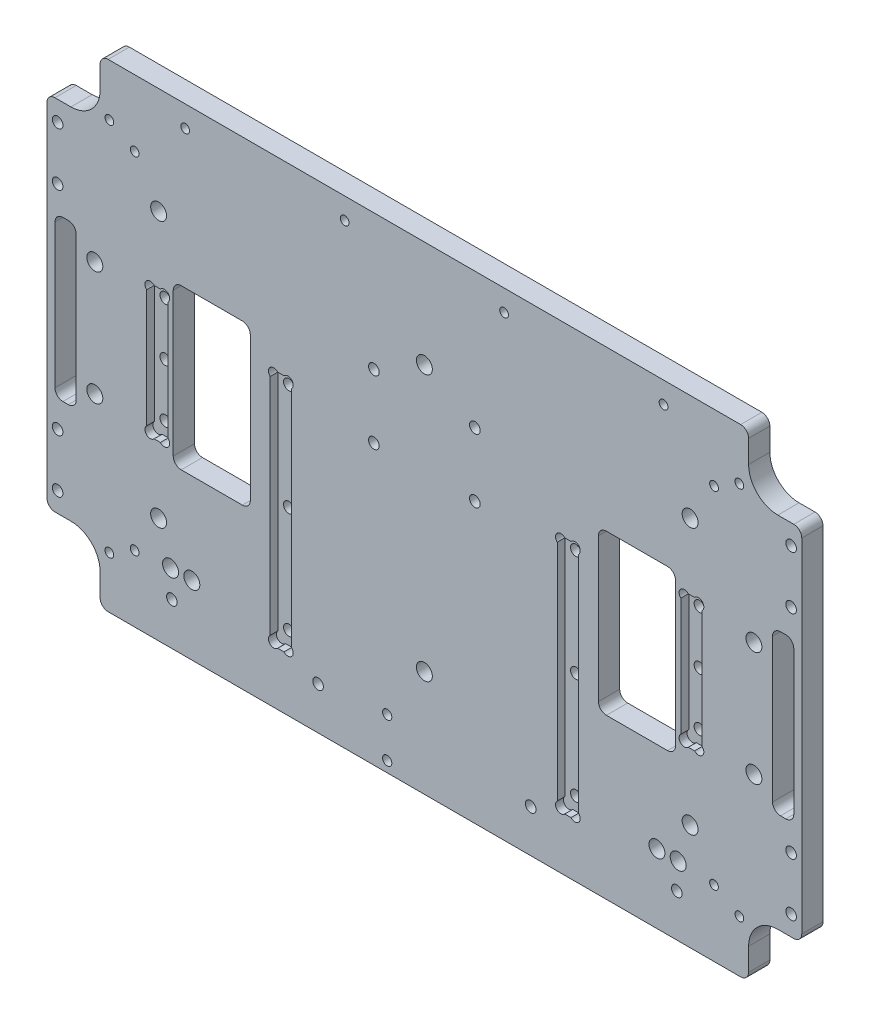
SolidWorks part; units mm, degrees
ref_plane "Front" through (0, 0, 0) normal (0, 0, 1) x (1, 0, 0)
ref_plane "Top" through (0, 0, 0) normal (0, 1, 0) x (1, 0, 0)
ref_plane "Right" through (0, 0, 0) normal (1, 0, 0) x (0, 0, -1)
sketch "Esquisse1" plane through (0, 0, 0) normal (0, 0, 1) x (1, 0, 0)
  line L1 (0, 0) -> (284, 0)
  line L2 (0, 0) -> (0, 180)
  line L3 (0, 180) -> (284, 180)
  line L4 (284, 0) -> (284, 180)
  dimension "D1" = 284
  dimension "D2" = 180
extrude "Boss.-Extru.1" add sketch "Esquisse1" along normal blind 8
sketch "Esquisse2" plane through (0, 0, 8) normal (0, 0, 1) x (1, 0, 0)
  line L0 (142, 180) -> (142, 0) construction
  line L1 (47.5, 60) -> (76.5, 60)
  line L2 (47.5, 60) -> (47.5, 120)
  line L3 (47.5, 120) -> (76.5, 120)
  line L4 (76.5, 60) -> (76.5, 120)
  line L5 (284, 180) -> (0, 180) construction
  line L6 (0, 0) -> (284, 0) construction
  line L7 (76.5, 90) -> (142, 90) construction
  line L8 (62, 60) -> (62, 120) construction
  line L9 (47.5, 90) -> (11, 90) construction
  line L10 (7, 60) -> (7, 120) construction
  line L11 (3, 60) -> (11, 60)
  line L12 (3, 60) -> (3, 120)
  line L13 (3, 120) -> (11, 120)
  line L14 (11, 60) -> (11, 120)
  line L15 (277, 60) -> (277, 120) construction
  line L16 (236.5, 90) -> (273, 90) construction
  line L17 (222, 60) -> (222, 120) construction
  line L18 (273, 60) -> (273, 120)
  line L19 (281, 120) -> (273, 120)
  line L20 (281, 60) -> (281, 120)
  line L21 (281, 60) -> (273, 60)
  line L22 (207.5, 60) -> (207.5, 120)
  line L23 (236.5, 120) -> (207.5, 120)
  line L24 (236.5, 60) -> (236.5, 120)
  line L25 (236.5, 60) -> (207.5, 60)
  dimension "D1" = 90
  dimension "D2" = 60
  dimension "D3" = 29
  dimension "D4" = 160
  dimension "D5" = 8
  dimension "D6" = 60
  dimension "D7" = 270
extrude "Enlèv. mat.-Extru.1" cut sketch "Esquisse2" against normal through all
sketch "Esquisse3" plane through (0, 0, 8) normal (0, 0, 1) x (1, 0, 0)
  line L0 (0, 172) -> (284, 172) construction
  line L1 (0, 180) -> (0, 0) construction
  line L2 (284, 0) -> (284, 180) construction
  line L3 (112, 172) -> (112, 180.3897) construction
  line L5 (172, 172) -> (172, 180.3897) construction
  line L6 (172, 180.3897) -> (112, 180.3897) construction
  line L7 (142, 180.3897) -> (142, 180) construction
  line L8 (284, 180) -> (0, 180) construction
  circle A0 centre (112, 172) radius 1.65
  circle A1 centre (172, 172) radius 1.65
  circle A2 centre (232, 172) radius 1.65
  circle A4 centre (52, 172) radius 1.65
  dimension "D1" = 3.3
  dimension "D2" = 4
  dimension "D3" = 8
  dimension "D4" = 60
extrude "Enlèv. mat.-Extru.2" cut sketch "Esquisse3" against normal up to vertex (8 mm away) up to point (284, 180, 0)
sketch "Esquisse4" plane through (0, 0, 8) normal (0, 0, 1) x (1, 0, 0)
  line L0 (142, 0) -> (142, 180) construction
  line L1 (84, 110) -> (92, 110)
  line L2 (84, 110) -> (84, 20)
  line L3 (84, 20) -> (92, 20)
  line L4 (92, 110) -> (92, 20)
  line L5 (0, 0) -> (284, 0) construction
  line L6 (284, 180) -> (0, 180) construction
  line L8 (76.5, 60) -> (76.5, 120) construction
  line L9 (192, 110) -> (192, 20)
  line L10 (200, 20) -> (192, 20)
  line L11 (200, 110) -> (200, 20)
  line L12 (200, 110) -> (192, 110)
  line L13 (47.5, 120) -> (47.5, 60) construction
  line L14 (37.5, 115) -> (45.5, 115)
  line L15 (37.5, 115) -> (37.5, 65)
  line L16 (37.5, 65) -> (45.5, 65)
  line L17 (45.5, 115) -> (45.5, 65)
  line L18 (45.5, 90) -> (47.5, 90) construction
  line L19 (238.5, 90) -> (236.5, 90) construction
  line L20 (238.5, 115) -> (238.5, 65)
  line L21 (246.5, 65) -> (238.5, 65)
  line L22 (246.5, 115) -> (246.5, 65)
  line L23 (246.5, 115) -> (238.5, 115)
  line L24 (47.5, 60) -> (76.5, 60) construction
  dimension "D1" = 40
  dimension "D2" = 90
  dimension "D3" = 8
  dimension "D4" = 7.5
  dimension "D5" = 8
  dimension "D6" = 2
  dimension "D7" = 50
extrude "Enlèv. mat.-Extru.3" cut sketch "Esquisse4" against normal blind 3
sketch "Esquisse5" plane through (0, 0, 8) normal (0, 0, 1) x (1, 0, 0)
  line L0 (142, 0) -> (142, 124.0722) construction
  line L2 (142, 117) -> (121.1311, 117) construction
  line L3 (0, 180) -> (0, 0) construction
  circle A0 centre (123, 129) radius 2
  circle A1 centre (123, 105) radius 2
  circle A2 centre (161, 105) radius 2
  circle A3 centre (161, 129) radius 2
  circle A5 centre (112, 172) radius 1.65 construction
  dimension "D1" = 38
  dimension "D2" = 4
  dimension "D3" = 24
  dimension "D4" = 55
  dimension "D5" = 142
extrude "Enlèv. mat.-Extru.4" cut sketch "Esquisse5" against normal through all
sketch "Esquisse6" plane through (0, 0, 8) normal (0, 0, 1) x (1, 0, 0)
  line L0 (142, 0) -> (142, 119.0936) construction
  line L1 (0, 0) -> (284, 0) construction
  line L2 (11, 90) -> (29.8915, 90) construction
  line L4 (11, 60) -> (11, 120) construction
  line L5 (273, 90) -> (254.1085, 90) construction
  circle A0 centre (18, 111.5) radius 3
  circle A1 centre (18, 68.5) radius 3
  circle A2 centre (266, 68.5) radius 3
  circle A3 centre (266, 111.5) radius 3
  dimension "D3" = 6
  dimension "D1" = 21.5
  dimension "D2" = 7
extrude "Enlèv. mat.-Extru.5" cut sketch "Esquisse6" against normal through all
sketch "Esquisse8" plane through (0, 0, 8) normal (0, 0, 1) x (1, 0, 0)
  line L0 (142, 180) -> (142, 109.7669) construction
  line L1 (0, 180) -> (20, 180)
  line L2 (0, 180) -> (0, 157.5)
  line L3 (0, 157.5) -> (20, 157.5)
  line L4 (20, 180) -> (20, 157.5)
  line L5 (284, 180) -> (0, 180) construction
  line L6 (264, 180) -> (264, 157.5)
  line L7 (284, 157.5) -> (264, 157.5)
  line L8 (284, 180) -> (284, 157.5)
  line L9 (284, 180) -> (264, 180)
  line L10 (264, 0) -> (264, 22.5)
  line L11 (0, 0) -> (20, 0)
  line L12 (0, 0) -> (0, 22.5)
  line L13 (0, 22.5) -> (20, 22.5)
  line L14 (20, 0) -> (20, 22.5)
  line L15 (284, 22.5) -> (264, 22.5)
  line L16 (284, 0) -> (284, 22.5)
  line L17 (284, 0) -> (264, 0)
  dimension "D1" = 22.5
  dimension "D2" = 20
  dimension "D3" = 22.5
extrude "Enlèv. mat.-Extru.7" cut sketch "Esquisse8" against normal through all
fillet "Congé1" radius 11 4 edges at (20, 157.5, 4) (264, 157.5, 4) (264, 22.5, 4) (20, 22.5, 4)
sketch "Esquisse7" plane through (0, 0, 8) normal (0, 0, 1) x (1, 0, 0)
  line L0 (142, 180) -> (142, 7.3256) construction
  line L1 (264, 180) -> (20, 180) construction
  line L2 (23.4737, 160.5) -> (33, 155) construction
  line L3 (264, 180) -> (20, 180) construction
  line L4 (260.5263, 160.5) -> (251, 155) construction
  line L5 (33, 155) -> (33, 25) construction
  line L6 (33, 90) -> (100.6533, 90) construction
  line L7 (23.4737, 19.5) -> (33, 25) construction
  line L8 (20, 0) -> (264, 0) construction
  line L9 (260.5263, 19.5) -> (251, 25) construction
  circle A0 centre (33, 155) radius 1.65
  circle A1 centre (23.4737, 160.5) radius 1.65
  circle A2 centre (260.5263, 160.5) radius 1.65
  circle A3 centre (251, 155) radius 1.65
  circle A5 centre (23.4737, 19.5) radius 1.65
  circle A6 centre (33, 25) radius 1.65
  circle A7 centre (251, 25) radius 1.65
  circle A8 centre (260.5263, 19.5) radius 1.65
  dimension "D1" = 3.3
  dimension "D5" = 25
  dimension "D2" = 11
  dimension "D3" = 109
  dimension "D4" = 30
  dimension "D6" = 25
extrude "Enlèv. mat.-Extru.6" cut sketch "Esquisse7" against normal through all
fillet "Congé2" radius 3 16 edges at (281, 60, 4) (273, 60, 4) (281, 120, 4) (273, 120, 4) (236.5, 120, 4) (207.5, 120, 4) (236.5, 60, 4) (207.5, 60, 4) (76.5, 60, 4) (47.5, 60, 4) (76.5, 120, 4) (47.5, 120, 4) (11, 120, 4) (3, 120, 4) (3, 60, 4) (11, 60, 4)
sketch "Esquisse9" plane through (0, 0, 8) normal (0, 0, 1) x (1, 0, 0)
  line L0 (37.5, 115) -> (38.8435, 113.6565) construction
  line L1 (45.5, 115) -> (37.5, 115) construction
  line L2 (41.5, 115) -> (41.5, 118.2808) construction
  line L3 (45.5, 115) -> (37.5, 115) construction
  line L4 (45.5, 115) -> (44.1565, 113.6565) construction
  line L5 (45.5, 90) -> (42.8729, 90) construction
  line L6 (45.5, 65) -> (45.5, 115) construction
  line L7 (45.5, 65) -> (44.1565, 66.3435) construction
  line L8 (37.5, 65) -> (38.8435, 66.3435) construction
  line L9 (45.5, 90) -> (238.5, 90) construction
  line L10 (238.5, 115) -> (238.5, 65) construction
  line L11 (142, 90) -> (142, 121.5895) construction
  line L12 (246.5, 65) -> (245.1565, 66.3435) construction
  line L13 (238.5, 65) -> (239.8435, 66.3435) construction
  line L14 (238.5, 90) -> (241.1271, 90) construction
  line L15 (238.5, 115) -> (239.8435, 113.6565) construction
  line L16 (242.5, 115) -> (242.5, 118.2808) construction
  line L17 (246.5, 115) -> (245.1565, 113.6565) construction
  line L18 (84, 110) -> (85.3435, 108.6565) construction
  line L19 (92, 110) -> (84, 110) construction
  line L20 (88, 110) -> (88, 112.2434) construction
  line L21 (92, 110) -> (84, 110) construction
  line L22 (92, 110) -> (90.6565, 108.6565) construction
  line L23 (84, 65) -> (89.3356, 65) construction
  line L24 (84, 110) -> (84, 20) construction
  line L25 (92, 20) -> (90.6565, 21.3435) construction
  line L26 (88, 20) -> (88, 17.7566) construction
  line L27 (84, 20) -> (85.3435, 21.3435) construction
  line L28 (200, 20) -> (198.6565, 21.3435) construction
  line L29 (196, 20) -> (196, 17.7566) construction
  line L30 (192, 20) -> (193.3435, 21.3435) construction
  line L31 (200, 65) -> (194.6644, 65) construction
  line L32 (192, 110) -> (193.3435, 108.6565) construction
  line L33 (196, 110) -> (196, 112.2434) construction
  line L34 (200, 110) -> (198.6565, 108.6565) construction
  circle A0 centre (38.8435, 113.6565) radius 2
  circle A1 centre (44.1565, 113.6565) radius 2
  circle A2 centre (44.1565, 66.3435) radius 2
  circle A3 centre (38.8435, 66.3435) radius 2
  circle A4 centre (245.1565, 66.3435) radius 2
  circle A5 centre (239.8435, 66.3435) radius 2
  circle A6 centre (239.8435, 113.6565) radius 2
  circle A7 centre (245.1565, 113.6565) radius 2
  circle A8 centre (85.3435, 108.6565) radius 2
  circle A9 centre (90.6565, 108.6565) radius 2
  circle A10 centre (90.6565, 21.3435) radius 2
  circle A11 centre (85.3435, 21.3435) radius 2
  circle A12 centre (198.6565, 21.3435) radius 2
  circle A13 centre (193.3435, 21.3435) radius 2
  circle A14 centre (193.3435, 108.6565) radius 2
  circle A15 centre (198.6565, 108.6565) radius 2
  dimension "D1" = 4
  dimension "D6" = 4
  dimension "D2" = 45
  dimension "D3" = 1.9
  dimension "D4" = 45
  dimension "D5" = 1.9
extrude "Enlèv. mat.-Extru.8" cut sketch "Esquisse9" against normal up to vertex (3 mm away)
fillet "Congé3" radius 3 8 edges at (264, 180, 4) (284, 157.5, 4) (284, 22.5, 4) (264, 0, 4) (20, 0, 4) (0, 22.5, 4) (0, 157.5, 4) (20, 180, 4)
sketch "Esquisse10" plane through (0, 0, 5) normal (0, 0, 1) x (1, 0, 0)
  line L0 (41.5, 115) -> (41.5, 65) construction
  line L1 (42.6749, 115) -> (40.3251, 115) construction
  line L2 (40.3251, 65) -> (42.6749, 65) construction
  line L3 (41.5, 90) -> (37.5, 90) construction
  line L4 (37.5, 112.1749) -> (37.5, 67.8251) construction
  line L5 (88, 110) -> (88, 20) construction
  line L6 (89.1749, 110) -> (86.8251, 110) construction
  line L7 (86.8251, 20) -> (89.1749, 20) construction
  line L8 (88, 65) -> (84, 65) construction
  line L9 (84, 107.1749) -> (84, 22.8251) construction
  line L10 (142, 0) -> (142, 180) construction
  line L11 (23, 0) -> (261, 0) construction
  line L12 (261, 180) -> (23, 180) construction
  line L13 (196, 65) -> (200, 65) construction
  line L14 (196, 110) -> (196, 20) construction
  line L15 (242.5, 90) -> (246.5, 90) construction
  line L16 (242.5, 115) -> (242.5, 65) construction
  circle A0 centre (41.5, 90) radius 2
  circle A1 centre (41.5, 70) radius 2
  circle A2 centre (41.5, 110) radius 2
  circle A3 centre (88, 65) radius 2
  circle A4 centre (88, 25) radius 2
  circle A5 centre (88, 105) radius 2
  circle A6 centre (196, 105) radius 2
  circle A7 centre (196, 25) radius 2
  circle A8 centre (196, 65) radius 2
  circle A9 centre (242.5, 110) radius 2
  circle A10 centre (242.5, 70) radius 2
  circle A11 centre (242.5, 90) radius 2
  dimension "D1" = 4
  dimension "D2" = 20
  dimension "D3" = 40
extrude "Enlèv. mat.-Extru.9" cut sketch "Esquisse10" against normal through all
sketch "Esquisse11" plane through (0, 0, 8) normal (0, 0, 1) x (1, 0, 0)
  line L0 (142, 0) -> (142, 52.4414) construction
  line L1 (23, 0) -> (261, 0) construction
  line L2 (142, 16) -> (47, 16) construction
  line L3 (86.8251, 20) -> (89.1749, 20) construction
  line L4 (46.5, 26) -> (54.5, 26) construction
  line L5 (237.5, 26) -> (229.5, 26) construction
  circle A0 centre (47, 16) radius 2
  circle A1 centre (237, 16) radius 2
  circle A2 centre (102, 16) radius 2
  circle A3 centre (46.5, 26) radius 3
  circle A4 centre (54.5, 26) radius 3
  circle A5 centre (229.5, 26) radius 3
  circle A6 centre (237.5, 26) radius 3
  circle A7 centre (182, 16) radius 2
  point P10 (94.5, 16)
  point P13 (88, 20)
  dimension "D1" = 4
  dimension "D2" = 190
  dimension "D4" = 8
  dimension "D5" = 10
  dimension "D7" = 6
  dimension "D8" = 80
  dimension "D3" = 4
  dimension "D6" = 87.5
extrude "Enlèv. mat.-Extru.10" cut sketch "Esquisse11" against normal through all
sketch "Esquisse12" plane through (0, 0, 8) normal (0, 0, 1) x (1, 0, 0)
  line L0 (128, 0) -> (128, 19) construction
  line L1 (23, 0) -> (261, 0) construction
  circle A0 centre (128, 4) radius 1.75
  circle A1 centre (128, 19) radius 1.75
  dimension "D1" = 15
  dimension "D2" = 3.5
  dimension "D3" = 4
  dimension "D4" = 128
extrude "Enlèv. mat.-Extru.11" cut sketch "Esquisse12" against normal through all
sketch "Esquisse13" plane through (0, 0, 8) normal (0, 0, 1) x (1, 0, 0)
  line L0 (4, 157.5) -> (4, 22.5) construction
  line L1 (3, 157.5) -> (9, 157.5) construction
  line L2 (9, 22.5) -> (3, 22.5) construction
  line L3 (0, 154.5) -> (0, 25.5) construction
  line L4 (11, 90) -> (4, 90) construction
  line L5 (11, 63) -> (11, 117) construction
  line L6 (142, 0) -> (142, 180) construction
  line L7 (23, 0) -> (261, 0) construction
  line L8 (261, 180) -> (23, 180) construction
  line L9 (273, 90) -> (280, 90) construction
  line L10 (280, 157.5) -> (280, 22.5) construction
  circle A0 centre (4, 30) radius 2
  circle A1 centre (4, 50) radius 2
  circle A2 centre (4, 130) radius 2
  circle A3 centre (4, 150) radius 2
  circle A4 centre (280, 150) radius 2
  circle A5 centre (280, 130) radius 2
  circle A6 centre (280, 50) radius 2
  circle A7 centre (280, 30) radius 2
  dimension "D2" = 20
  dimension "D3" = 4
  dimension "D4" = 80
  dimension "D1" = 4
extrude "Enlèv. mat.-Extru.12" cut sketch "Esquisse13" against normal through all
sketch "Esquisse14" plane through (0, 0, 8) normal (0, 0, 1) x (1, 0, 0)
  line L0 (142, 0) -> (142, 180) construction
  line L1 (23, 0) -> (261, 0) construction
  line L2 (261, 180) -> (23, 180) construction
  line L3 (142, 90) -> (0, 90) construction
  line L4 (0, 154.5) -> (0, 25.5) construction
  line L5 (142, 40) -> (42, 40) construction
  circle A0 centre (42, 140) radius 3
  circle A1 centre (42, 40) radius 3
  circle A2 centre (242, 40) radius 3
  circle A3 centre (242, 140) radius 3
  circle A4 centre (142, 40) radius 3
  circle A5 centre (142, 140) radius 3
  dimension "D3" = 6
  dimension "D1" = 200
  dimension "D2" = 50
extrude "fixations_usinage" cut sketch "Esquisse14" against normal through all both and the other way through all
